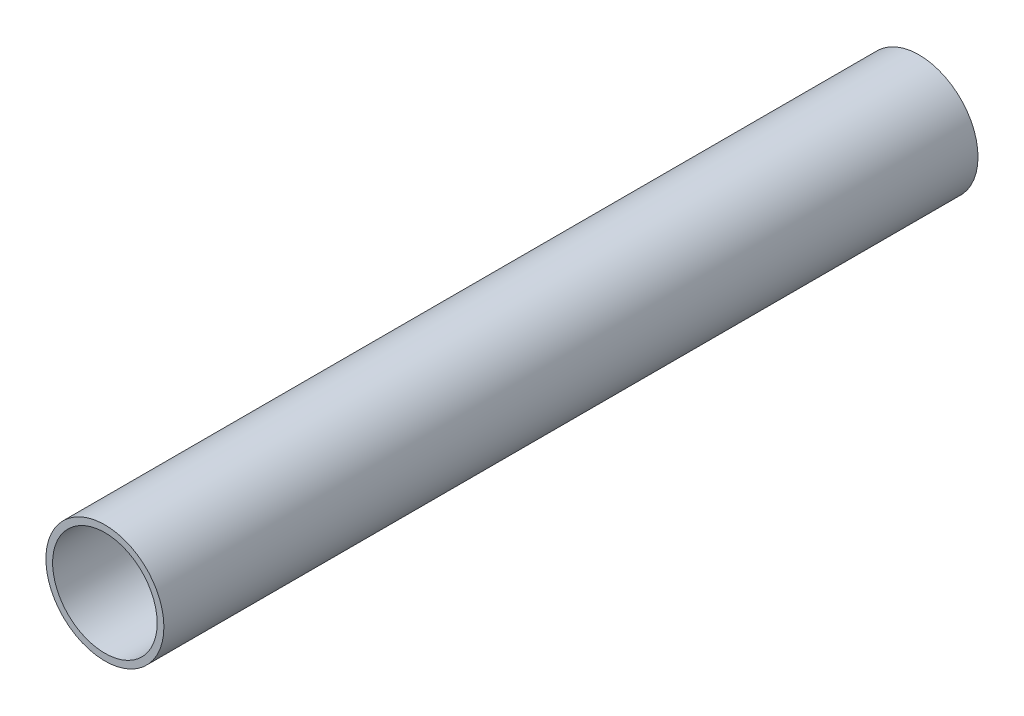
SolidWorks part; units mm, degrees
material "PLA"
ref_plane "Alzado" through (0, 0, 0) normal (0, 0, 1) x (1, 0, 0)
ref_plane "Planta" through (0, 0, 0) normal (0, 1, 0) x (1, 0, 0)
ref_plane "Vista lateral" through (0, 0, 0) normal (1, 0, 0) x (0, 0, -1)
sketch "Croquis1" plane through (0, 0, 0) normal (0, 0, 1) x (1, 0, 0)
  circle A0 centre (0, 0) radius 15.54
  circle A1 centre (0, 0) radius 17.54
  dimension "D1" = 35.08
  dimension "D2" = 31.08
extrude "Saliente-Extruir1" add sketch "Croquis1" along normal blind 242
equation "\"DouterAblative\"=35.08"
equation "\"D1@Croquis1\"=\"DouterAblative\""
equation "\"DinnerAblative\"= \"DouterAblative\" - \"AblativeThickness\" * 2"
equation "\"D2@Croquis1\"=\"DinnerAblative\""
equation "\"LengthAblative\"=242"
equation "\"D1@Saliente-Extruir1\"=\"LengthAblative\""
equation "\"AblativeThickness\"= 2"
